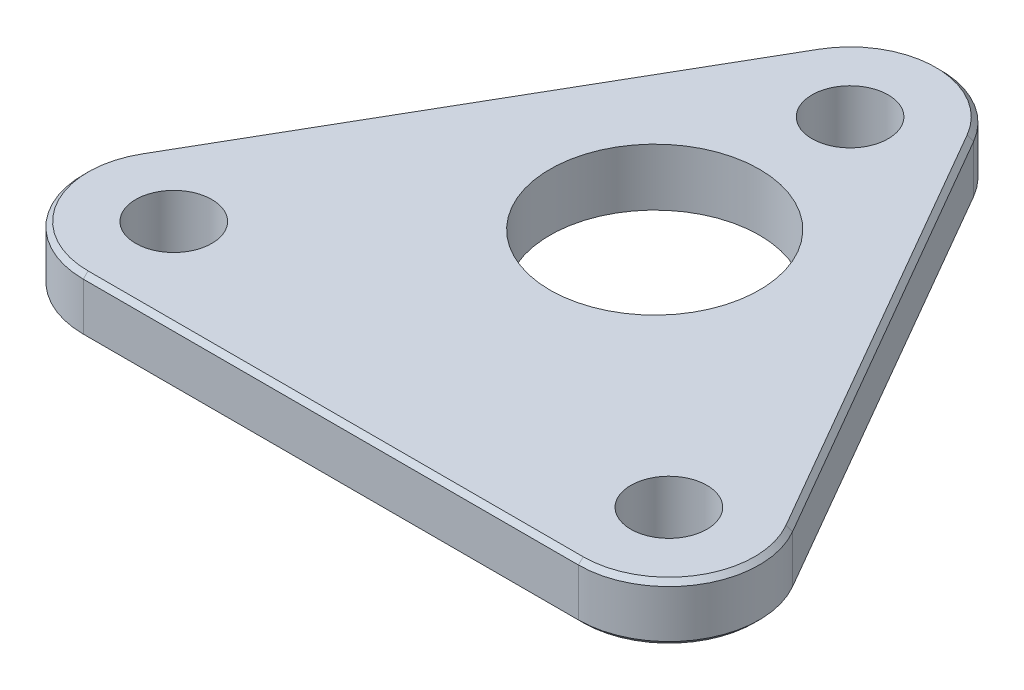
SolidWorks part; units mm, degrees
material "ﾒﾗﾐﾝ樹脂"
ref_plane "正面" through (0, 0, 0) normal (0, 0, 1) x (1, 0, 0)
ref_plane "平面" through (0, 0, 0) normal (0, 1, 0) x (1, 0, 0)
ref_plane "右側面" through (0, 0, 0) normal (1, 0, 0) x (0, 0, -1)
sketch "ｽｹｯﾁ1" plane through (0, 0, 0) normal (0, 1, 0) x (1, 0, 0)
  line L0 (-8.2272, 34.7722) -> (-34.2272, -10.2611)
  line L1 (34.2272, -10.2611) -> (8.2272, 34.7722)
  line L3 (-26, -24.5111) -> (26, -24.5111)
  circle A0 centre (0, 30.0222) radius 4
  circle A1 centre (0, 30.0222) radius 9.5
  circle A3 centre (26, -15.0111) radius 9.5
  circle A4 centre (26, -15.0111) radius 4
  circle A5 centre (-26, -15.0111) radius 9.5
  circle A6 centre (-26, -15.0111) radius 4
  point P15 (0, 0)
  point P18 (0, 0)
  dimension "D1" = 3
  dimension "D2" = 3
extrude "ﾎﾞｽ - 押し出し1" add sketch "ｽｹｯﾁ1" along normal blind 6 contours A5 L3 A3 L1 A1 L0 | A5 A6 | A3 A4 | A1 A0
chamfer "面取り1" distance 0.5 angle 45 12 edges at (34.2272, 0, 19.7611) (34.2272, 6, 19.7611) (21.2272, 0, -12.2556) (21.2272, 6, -12.2556) (0, 0, -39.5222) (0, 6, -39.5222) (-21.2272, 0, -12.2556) (-21.2272, 6, -12.2556) (-34.2272, 0, 19.7611) (-34.2272, 6, 19.7611) (0, 0, 24.5111) (0, 6, 24.5111)
sketch "ｽｹｯﾁ3" plane through (0, 0, 0) normal (0, -1, 0) x (1, 0, 0)
  circle A0 centre (0, -9.5) radius 15
extrude "ｶｯﾄ - 押し出し1" cut sketch "ｽｹｯﾁ3" against normal up to next
sketch "ｽｹｯﾁ4" plane through (0, 0, 0) normal (0, -1, 0) x (1, 0, 0)
  circle A0 centre (0, -9.5) radius 15
  circle A1 centre (0, -9.5) radius 13
extrude "ﾎﾞｽ - 押し出し2" add sketch "ｽｹｯﾁ4" against normal up to surface (6 mm away) up to face at (0, 6, 5.5)
sketch "ｽｹｯﾁ5" plane through (0, 0, 0) normal (0, -1, 0) x (1, 0, 0)
  circle A0 centre (0, -9.5) radius 13
  circle A1 centre (0, -9.5) radius 11
extrude "ﾎﾞｽ - 押し出し3" add sketch "ｽｹｯﾁ5" against normal up to surface (6 mm away) up to face at (0, 6, 0)
